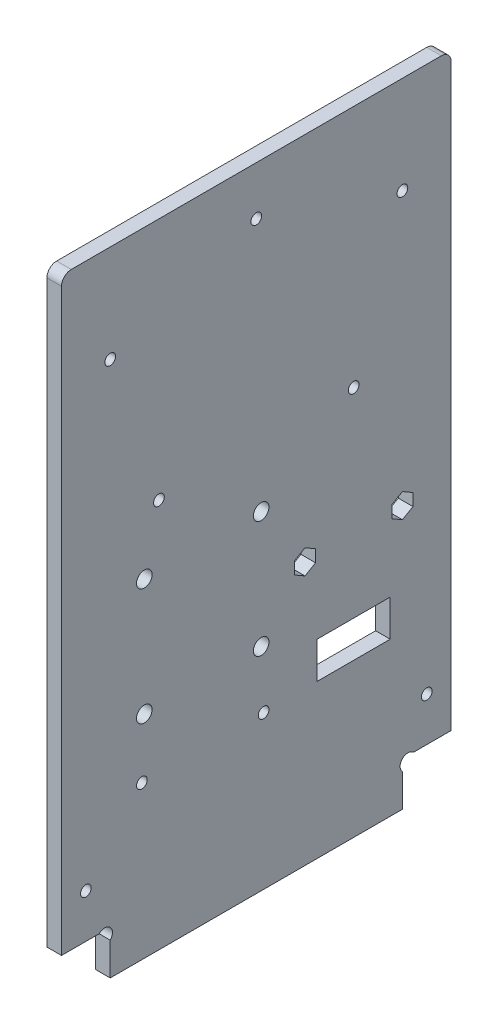
SolidWorks part; units mm, degrees
ref_plane "Plan de face" through (0, 0, 0) normal (0, 0, 1) x (1, 0, 0)
ref_plane "Plan de dessus" through (0, 0, 0) normal (0, 1, 0) x (1, 0, 0)
ref_plane "Plan de droite" through (0, 0, 0) normal (1, 0, 0) x (0, 0, -1)
sketch "Esquisse1" plane through (0, 0, 0) normal (1, 0, 0) x (0, 0, -1)
  line L8 (10, 6.7373) -> (10, 0)
  line L9 (70, 6.7373) -> (70, 0)
  line L10 (7.7373, 9) -> (0, 9)
  line L11 (10, 0) -> (70, 0)
  line L12 (72.2627, 9) -> (80, 9)
  line L13 (0, 9) -> (0, 130)
  line L14 (0, 130) -> (80, 130)
  line L15 (80, 130) -> (80, 9)
  arc A0 (10, 6.7373) -> (7.7373, 9) centre (8.8686, 7.8686) ccw
  arc A1 (70, 6.7373) -> (72.2627, 9) centre (71.1314, 7.8686) cw
  dimension "D7" = 1.1314
  dimension "D6" = 1.6
  dimension "D1" = 9
  dimension "D2" = 10
  dimension "D3" = 10
  dimension "D4" = 80
  dimension "D5" = 130
  dimension "D8" = 1.1314
  dimension "D9" = 1.1314
  dimension "D10" = 1.1314
extrude "Extrusion1" add sketch "Esquisse1" along normal blind 3
sketch "Esquisse2" plane through (3, 0, 0) normal (1, 0, 0) x (0, 0, -1)
  line L0 (0, 9) -> (7.7373, 9) construction
  line L1 (0, 130) -> (0, 9) construction
  line L2 (80, 9) -> (80, 130) construction
  line L3 (72.2627, 9) -> (80, 9) construction
  line L4 (80, 130) -> (0, 130) construction
  circle A0 centre (60, 80) radius 1.1
  circle A1 centre (10, 110) radius 1.1
  circle A2 centre (20, 80) radius 1.1
  circle A3 centre (70, 110) radius 1.1
  circle A4 centre (17, 67.45) radius 1.6
  circle A5 centre (17, 43.45) radius 1.6
  circle A6 centre (41, 43.45) radius 1.6
  circle A7 centre (41, 67.45) radius 1.6
  circle A8 centre (40, 120) radius 1.1
  circle A9 centre (70, 54) radius 1.1
  circle A10 centre (50, 54) radius 1.1
  dimension "D5" = 17
  dimension "D7" = 10
  dimension "D9" = 10
  dimension "D4" = 3.2
  dimension "D6" = 2.2
  dimension "D1" = 58.45
  dimension "D2" = 24
  dimension "D3" = 24
  dimension "D8" = 40
  dimension "D10" = 30
  dimension "D11" = 10
  dimension "D12" = 20
  dimension "D13" = 10
  dimension "D14" = 10
  dimension "D15" = 10
  dimension "D16" = 20
  dimension "D17" = 45
extrude "Enlèv. mat.-Extru.1" cut sketch "Esquisse2" against normal through all
sketch "Esquisse3" plane through (0, 0, 0) normal (-1, 0, 0) x (0, 0, 1)
  line L1 (-67.5, 39) -> (-52.5, 39)
  line L2 (-67.5, 39) -> (-67.5, 31.5)
  line L3 (-67.5, 31.5) -> (-52.5, 31.5)
  line L4 (-52.5, 39) -> (-52.5, 31.5)
  circle A0 centre (-70, 54) radius 1.1 construction
  circle A1 centre (-50, 54) radius 1.1 construction
  dimension "D4" = 2.5
  dimension "D1" = 15
  dimension "D2" = 7.5
  dimension "D3" = 15
  dimension "D5" = 2.5
extrude "Enlèv. mat.-Extru.2" cut sketch "Esquisse3" against normal through all
sketch "Esquisse4" plane through (3, 0, 0) normal (1, 0, 0) x (0, 0, -1)
  line L3 (0, 9) -> (7.7373, 9) construction
  line L4 (0, 130) -> (0, 9) construction
  line L5 (80, 9) -> (80, 130) construction
  circle A2 centre (75, 18) radius 1.1
  circle A3 centre (5, 18) radius 1.1
  dimension "D1" = 2.2
  dimension "D2" = 5
  dimension "D3" = 5
  dimension "D5" = 9
extrude "Enlèv. mat.-Extru.3" cut sketch "Esquisse4" against normal through all
sketch "Esquisse5" plane through (3, 0, 0) normal (1, 0, 0) x (0, 0, -1)
  line L0 (80, 9) -> (80, 130) construction
  line L1 (50, 51.5) -> (52.1651, 52.75)
  line L2 (52.1651, 52.75) -> (52.1651, 55.25)
  line L3 (52.1651, 55.25) -> (50, 56.5)
  line L4 (50, 56.5) -> (47.8349, 55.25)
  line L5 (47.8349, 55.25) -> (47.8349, 52.75)
  line L6 (47.8349, 52.75) -> (50, 51.5)
  line L7 (70, 51.5) -> (72.1651, 52.75)
  line L8 (72.1651, 52.75) -> (72.1651, 55.25)
  line L9 (72.1651, 55.25) -> (70, 56.5)
  line L10 (70, 56.5) -> (67.8349, 55.25)
  line L11 (67.8349, 55.25) -> (67.8349, 52.75)
  line L12 (67.8349, 52.75) -> (70, 51.5)
  circle A0 centre (50, 54) radius 2.1651 construction
  circle A1 centre (70, 54) radius 2.1651 construction
  dimension "D1" = 2.5
  dimension "D2" = 2.5
extrude "Enlèv. mat.-Extru.4" cut sketch "Esquisse5" against normal through all
fillet "Congé1" radius 2 2 edges at (1.5, 130, -80) (1.5, 130, 0)
sketch "Esquisse6" plane through (3, 0, 0) normal (1, 0, 0) x (0, 0, -1)
  line L0 (17, 43.45) -> (17, 35.9367) construction
  line L1 (41, 43.45) -> (41, 36.8364) construction
  circle A0 centre (16.5, 31.4604) radius 1.1
  circle A1 centre (41.5, 31.4604) radius 1.1
  dimension "D1" = 2.2
  dimension "D4" = 24
  dimension "D2" = 0.5
  dimension "D3" = 12
  dimension "D5" = 0.5
extrude "Enlèv. mat.-Extru.5" cut sketch "Esquisse6" against normal through all
